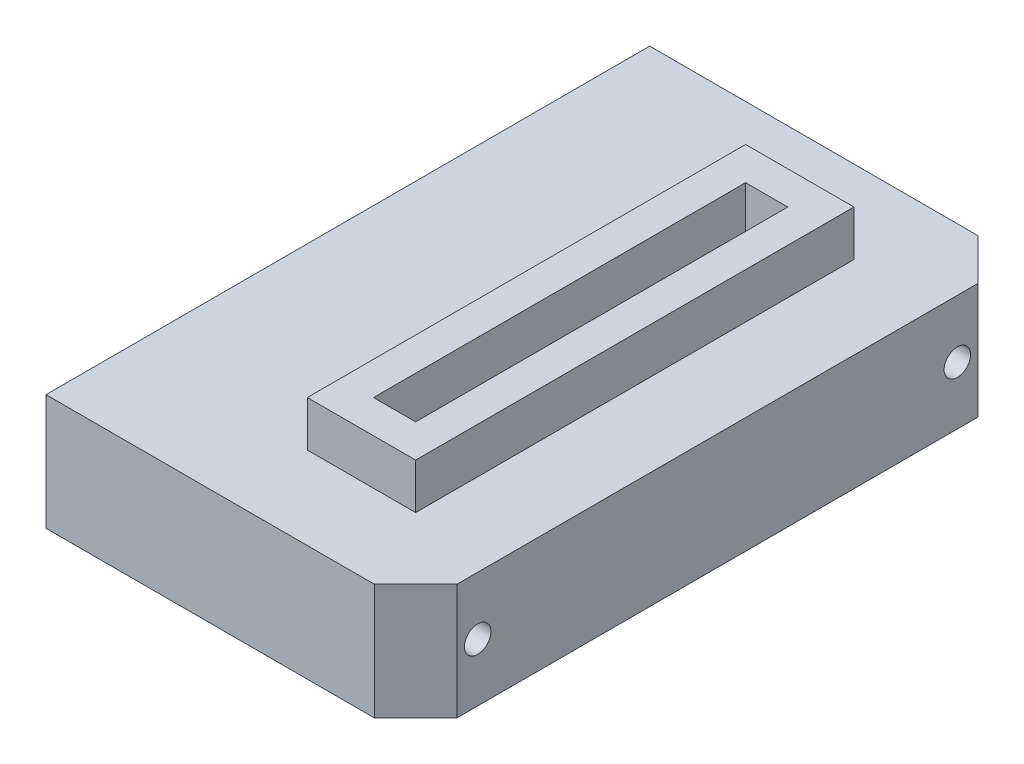
SolidWorks part; units mm, degrees
ref_plane "Front Plane" through (0, 0, 0) normal (0, 0, 1) x (1, 0, 0)
ref_plane "Top Plane" through (0, 0, 0) normal (0, 1, 0) x (1, 0, 0)
ref_plane "Right Plane" through (0, 0, 0) normal (1, 0, 0) x (0, 0, -1)
sketch "Sketch1" plane through (0, 0, 0) normal (0, 1, 0) x (1, 0, 0)
  line L1 (-22.0659, 27.9603) -> (22.6341, 27.9603)
  line L2 (-22.0659, 27.9603) -> (-22.0659, -45.0397)
  line L3 (-22.0659, -45.0397) -> (22.6341, -45.0397)
  line L4 (22.6341, 27.9603) -> (22.6341, -45.0397)
  line L5 (3.5341, 13.9603) -> (8.6341, 13.9603)
  line L6 (3.5341, 13.9603) -> (3.5341, -31.0397)
  line L7 (3.5341, -31.0397) -> (8.6341, -31.0397)
  line L8 (8.6341, 13.9603) -> (8.6341, -31.0397)
  dimension "D1" = 73
  dimension "D2" = 44.7
  dimension "D3" = 14
  dimension "D4" = 5.1
  dimension "D5" = 45
  dimension "D6" = 14
extrude "Boss-Extrude1" add sketch "Sketch1" along normal blind 14
sketch "Sketch2" plane through (22.6341, 0, 0) normal (1, 0, 0) x (0, 0, -1)
  line L0 (-45.0397, 14) -> (-45.0397, 0) construction
  line L2 (27.9603, 14) -> (27.9603, 0) construction
  line L5 (27.9603, 7) -> (12.9603, 7) construction
  line L6 (-45.0397, 7) -> (-30.0397, 7) construction
  circle A2 centre (-37.5397, 7) radius 1.6
  circle A3 centre (20.4603, 7) radius 1.6
  dimension "D3" = 3.2
  dimension "D4" = 3.2
  dimension "D1" = 15
  dimension "D2" = 15
extrude "Cut-Extrude1" cut sketch "Sketch2" against normal up to next
sketch "Sketch3" plane through (0, 14, 0) normal (0, 1, 0) x (1, 0, 0)
  line L0 (8.6341, -31.0397) -> (8.6341, 13.9603) construction
  line L1 (-0.4659, 17.9603) -> (12.6341, 17.9603)
  line L2 (-0.4659, 17.9603) -> (-0.4659, -35.0397)
  line L3 (-0.4659, -35.0397) -> (12.6341, -35.0397)
  line L4 (12.6341, 17.9603) -> (12.6341, -35.0397)
  line L5 (3.5341, 13.9603) -> (3.5341, -31.0397) construction
  line L6 (8.6341, 13.9603) -> (3.5341, 13.9603) construction
  line L7 (3.5341, -31.0397) -> (8.6341, -31.0397) construction
  line L9 (3.5341, 13.9603) -> (8.6341, 13.9603)
  line L10 (3.5341, 13.9603) -> (3.5341, -31.0397)
  line L11 (3.5341, -31.0397) -> (8.6341, -31.0397)
  line L12 (8.6341, 13.9603) -> (8.6341, -31.0397)
  dimension "D1" = 4
  dimension "D2" = 4
  dimension "D3" = 4
  dimension "D4" = 4
extrude "Boss-Extrude2" add sketch "Sketch3" along normal blind 5.5
sketch "Sketch4" plane through (0, 14, 0) normal (0, 1, 0) x (1, 0, 0)
  line L0 (17.6341, 27.9603) -> (22.6341, 22.9603)
  line L1 (22.6341, 27.9603) -> (17.6341, 27.9603)
  line L2 (22.6341, 27.9603) -> (22.6341, 22.9603)
  line L5 (17.6341, -45.0397) -> (22.6341, -40.0397)
  line L6 (22.6341, -45.0397) -> (17.6341, -45.0397)
  line L7 (22.6341, -45.0397) -> (22.6341, -40.0397)
  dimension "D1" = 5
extrude "Cut-Extrude2" cut sketch "Sketch4" against normal up to next
